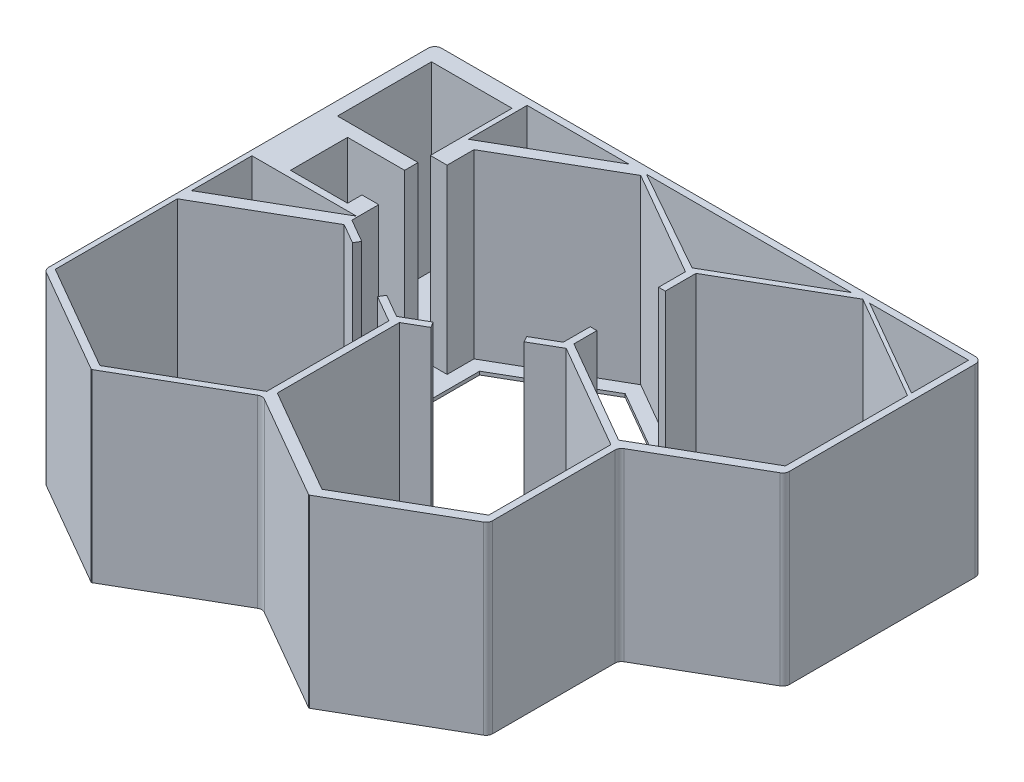
SolidWorks part; units mm, degrees
ref_plane "Front Plane" through (0, 0, 0) normal (0, 0, 1) x (1, 0, 0)
ref_plane "Top Plane" through (0, 0, 0) normal (0, 1, 0) x (1, 0, 0)
ref_plane "Right Plane" through (0, 0, 0) normal (1, 0, 0) x (0, 0, -1)
sketch "Sketch1" plane through (0, 0, 0) normal (0, 1, 0) x (1, 0, 0)
  line L1 (0, 0) -> (207.01, 0)
  line L2 (0, 0) -> (0, -171.45)
  line L3 (0, -171.45) -> (207.01, -171.45)
  line L4 (207.01, 0) -> (207.01, -171.45)
  dimension "D1" = 171.45
  dimension "D2" = 207.01
extrude "Boss-Extrude1" add sketch "Sketch1" along normal blind 69.85
sketch "Sketch3" plane through (0, 69.85, 0) normal (0, 1, 0) x (1, 0, 0)
  line L0 (1.905, -93.98) -> (41.4997, -71.12)
  line L1 (41.91, -76.2301) -> (1.905, -99.327)
  line L2 (1.905, -99.327) -> (1.905, -145.5208)
  line L3 (1.905, -145.5208) -> (41.91, -168.6177)
  line L4 (41.91, -168.6177) -> (81.915, -145.5208)
  line L5 (81.915, -145.5208) -> (81.915, -99.327)
  line L6 (81.915, -99.327) -> (71.8462, -93.5138)
  line L7 (81.915, -96.3941) -> (90.7138, -91.3141)
  line L8 (121.92, -73.2972) -> (121.92, -63.1372)
  line L9 (121.92, -27.1034) -> (81.915, -4.0065)
  line L10 (81.915, -4.0065) -> (41.91, -27.1034)
  line L11 (41.91, -27.1034) -> (41.91, -37.2634)
  line L12 (41.91, -73.2972) -> (50.7088, -78.3772)
  line L13 (124.46, -74.7636) -> (114.3912, -80.5769)
  line L14 (84.455, -97.8605) -> (84.455, -144.0543)
  line L15 (84.455, -144.0543) -> (124.46, -167.1512)
  line L16 (124.46, -167.1512) -> (164.465, -144.0543)
  line L17 (164.465, -144.0543) -> (164.465, -97.8605)
  line L18 (164.465, -97.8605) -> (124.46, -74.7636)
  line L25 (204.47, -25.6369) -> (164.465, -2.54)
  line L26 (164.465, -2.54) -> (124.46, -25.6369)
  line L27 (124.46, -25.6369) -> (124.46, -37.2634)
  line L28 (124.46, -71.8307) -> (164.465, -94.9276)
  line L29 (164.465, -94.9276) -> (204.47, -71.8307)
  line L30 (204.47, -71.8307) -> (204.47, -25.6369)
  line L31 (5.08, -6.35) -> (35.56, -6.35)
  line L32 (5.08, -6.35) -> (5.08, -41.91)
  line L33 (5.08, -41.91) -> (35.56, -41.91)
  line L34 (35.56, -6.35) -> (35.56, -37.2634)
  line L39 (13.97, -46.99) -> (35.56, -46.99)
  line L40 (13.97, -46.99) -> (13.97, -68.58)
  line L41 (13.97, -68.58) -> (35.56, -68.58)
  line L42 (35.56, -63.1372) -> (35.56, -68.58)
  line L43 (207.01, -171.45) -> (207.01, 0) construction
  line L44 (207.01, 0) -> (0, 0) construction
  line L49 (35.56, -37.2634) -> (41.91, -37.2634)
  line L50 (35.56, -41.91) -> (35.56, -46.99)
  line L51 (41.91, -63.1372) -> (35.56, -63.1372)
  line L52 (41.91, -63.1372) -> (41.91, -73.2972)
  line L53 (121.92, -37.2634) -> (124.46, -37.2634)
  line L54 (121.92, -63.1372) -> (124.46, -63.1372)
  line L55 (49.4388, -80.5769) -> (50.7088, -78.3772)
  line L56 (124.46, -63.1372) -> (124.46, -71.8307)
  line L57 (71.8462, -93.5138) -> (73.1162, -91.3141)
  line L58 (121.92, -37.2634) -> (121.92, -27.1034)
  line L59 (90.7138, -91.3141) -> (91.9838, -93.5138)
  line L60 (113.1212, -78.3772) -> (121.92, -73.2972)
  line L61 (113.1212, -78.3772) -> (114.3912, -80.5769)
  line L62 (91.9838, -93.5138) -> (84.455, -97.8605)
  line L63 (73.1162, -91.3141) -> (81.915, -96.3941)
  line L64 (49.4388, -80.5769) -> (41.91, -76.2301)
  line L65 (37.465, -24.765) -> (75.9598, -2.54)
  line L66 (75.9598, -2.54) -> (37.465, -2.54)
  line L67 (37.465, -2.54) -> (37.465, -24.765)
  line L68 (1.905, -93.98) -> (1.905, -71.12)
  line L69 (41.4997, -71.12) -> (1.905, -71.12)
  line L91 (167.075, -2.54) -> (204.47, -24.13)
  line L92 (204.47, -24.13) -> (204.47, -2.54)
  line L93 (204.47, -2.54) -> (167.075, -2.54)
  line L99 (82.646, -2.54) -> (121.92, -24.5925)
  line L100 (121.92, -24.5925) -> (160.116, -2.54)
  line L101 (160.116, -2.54) -> (82.646, -2.54)
  circle A0 centre (41.91, -122.4239) radius 40.005 construction
  circle A1 centre (81.915, -50.2003) radius 40.005 construction
  circle A2 centre (124.46, -120.9574) radius 40.005 construction
  circle A3 centre (164.465, -48.7338) radius 40.005 construction
  point P17 (61.9125, -157.0692)
  point P89 (24.765, -68.58)
  dimension "D1" = 80.01
  dimension "D25" = 180
  dimension "D2" = 35.56
  dimension "D3" = 30.48
  dimension "D6" = 80.01
  dimension "D7" = 80.01
  dimension "D8" = 80.01
  dimension "D9" = 21.59
  dimension "D10" = 21.59
  dimension "D11" = 2.54
  dimension "D12" = 82.563
  dimension "D13" = 2.54
  dimension "D14" = 42.545
  dimension "D15" = 2.54
  dimension "D16" = 2.54
  dimension "D17" = 2.54
  dimension "D18" = 143.0034
  dimension "D19" = 6.35
  dimension "D20" = 171.45
  dimension "D21" = 171.45
  dimension "D22" = 5.08
  dimension "D23" = 179.314
  dimension "D24" = 2.54
  dimension "D26" = 0
  dimension "D27" = 77.47
  dimension "D31" = 10.16
  dimension "D32" = 10.16
  dimension "D33" = 5.08
  dimension "D34" = 21.59
  dimension "D35" = 10.16
  dimension "D36" = 10.16
  dimension "D37" = 10.16
  dimension "D38" = 10.16
  dimension "D39" = 10.16
  dimension "D40" = 10.16
  dimension "D41" = 2.54
  dimension "D42" = 2.54
  dimension "D57" = 2.54
  dimension "D58" = 45.72
  dimension "D59" = 2.54
  dimension "D60" = 44.45
  dimension "D61" = 44.45
  dimension "D62" = 0
  dimension "D68" = 360
  dimension "D69" = 2.54
  dimension "D70" = 2.54
  dimension "D71" = 360
  dimension "D72" = 43.18
extrude "Cut-Extrude1" cut sketch "Sketch3" against normal blind 68.58
sketch "Sketch4" plane through (0, 69.85, 0) normal (0, 1, 0) x (1, 0, 0)
  line L0 (207.01, -74.3158) -> (167.005, -97.4127)
  line L1 (207.01, -171.45) -> (207.01, 0) construction
  line L2 (167.005, -97.4127) -> (167.005, -146.6017)
  line L3 (0, -171.45) -> (207.01, -171.45) construction
  line L4 (167.005, -171.45) -> (207.01, -171.45)
  line L5 (207.01, -171.45) -> (207.01, -74.3158)
  line L6 (164.465, -94.9276) -> (204.47, -71.8307) construction
  line L7 (164.465, -144.0543) -> (164.465, -97.8605) construction
  line L8 (0, -147.5382) -> (41.4164, -171.45)
  line L9 (41.6704, -171.45) -> (123.7124, -171.45)
  line L10 (0, 0) -> (0, -171.45) construction
  line L11 (0, -171.45) -> (207.01, -171.45) construction
  line L12 (41.4164, -171.45) -> (0, -171.45)
  line L13 (41.6704, -171.45) -> (82.6914, -147.7665)
  line L14 (82.6914, -147.7665) -> (123.7124, -171.45)
  line L16 (41.91, -168.6177) -> (81.915, -145.5208) construction
  line L17 (84.455, -144.0543) -> (124.46, -167.1512) construction
  line L18 (0, -171.45) -> (0, -147.5382)
  line L19 (1.905, -145.5208) -> (41.91, -168.6177) construction
  line L22 (123.9664, -171.45) -> (167.005, -146.6017)
  line L23 (121.92, -27.1034) -> (81.915, -4.0065) construction
  line L24 (1.905, -99.327) -> (1.905, -145.5208) construction
  line L28 (123.9664, -171.45) -> (167.005, -171.45)
  line L31 (81.915, -9.8723) -> (46.99, -30.0363)
  line L32 (46.99, -30.0363) -> (46.99, -70.3642)
  line L35 (164.465, -8.4059) -> (129.54, -28.5698)
  line L36 (129.54, -28.5698) -> (129.54, -68.8978)
  line L37 (129.54, -68.8978) -> (164.465, -89.0617)
  line L38 (164.465, -89.0617) -> (199.39, -68.8978)
  line L39 (199.39, -68.8978) -> (199.39, -28.5698)
  line L40 (199.39, -28.5698) -> (164.465, -8.4059)
  line L47 (41.91, -82.096) -> (6.985, -102.2599)
  line L48 (6.985, -102.2599) -> (6.985, -142.5879)
  line L49 (6.985, -142.5879) -> (41.91, -162.7518)
  line L50 (41.91, -162.7518) -> (76.835, -142.5879)
  line L51 (76.835, -142.5879) -> (76.835, -102.2599)
  line L52 (76.835, -102.2599) -> (41.91, -82.096)
  line L53 (41.91, -76.2301) -> (1.905, -99.327) construction
  line L54 (46.99, -70.3642) -> (81.915, -90.5282)
  line L55 (81.915, -90.5282) -> (116.84, -70.3642)
  line L56 (116.84, -70.3642) -> (116.84, -30.0363)
  line L57 (116.84, -30.0363) -> (81.915, -9.8723)
  line L58 (41.91, -27.1034) -> (41.91, -37.2634) construction
  line L59 (204.47, -25.6369) -> (164.465, -2.54) construction
  line L61 (164.465, -97.8605) -> (124.46, -74.7636) construction
  line L62 (124.46, -80.6295) -> (89.535, -100.7935)
  line L63 (89.535, -100.7935) -> (89.535, -141.1214)
  line L64 (89.535, -141.1214) -> (124.46, -161.2853)
  line L65 (124.46, -161.2853) -> (159.385, -141.1214)
  line L66 (159.385, -141.1214) -> (159.385, -100.7935)
  line L67 (159.385, -100.7935) -> (124.46, -80.6295)
  line L68 (124.46, -167.1512) -> (164.465, -144.0543) construction
  circle A0 centre (81.915, -50.2003) radius 34.925 construction
  circle A1 centre (164.465, -48.7338) radius 34.925 construction
  circle A2 centre (124.46, -120.9574) radius 34.925 construction
  circle A3 centre (41.91, -122.4239) radius 34.925 construction
  dimension "D14" = 40.005
  dimension "D1" = 180
  dimension "D2" = 2.54
  dimension "D3" = 180
  dimension "D4" = 0.254
  dimension "D5" = 0.254
  dimension "D6" = 125.5886
  dimension "D7" = 82.55
  dimension "D8" = 0
  dimension "D9" = 0
  dimension "D10" = 40.005
  dimension "D11" = 40.005
  dimension "D12" = 69.85
  dimension "D13" = 69.85
  dimension "D15" = 40.005
  dimension "D16" = 40.005
  dimension "D17" = 40.005
  dimension "D18" = 69.85
  dimension "D19" = 69.85
  dimension "D20" = 40.005
  dimension "D21" = 40.005
extrude "Cut-Extrude2" cut sketch "Sketch4" against normal through all both and the other way through all
fillet "Fillet3" radius 2.54 7 edges at (0, 34.925, 0) (0, 34.925, 147.5382) (82.6914, 34.925, 147.7665) (167.005, 34.925, 146.6017) (167.005, 34.925, 97.4127) (207.01, 34.925, 74.3158) (207.01, 34.925, 0)
